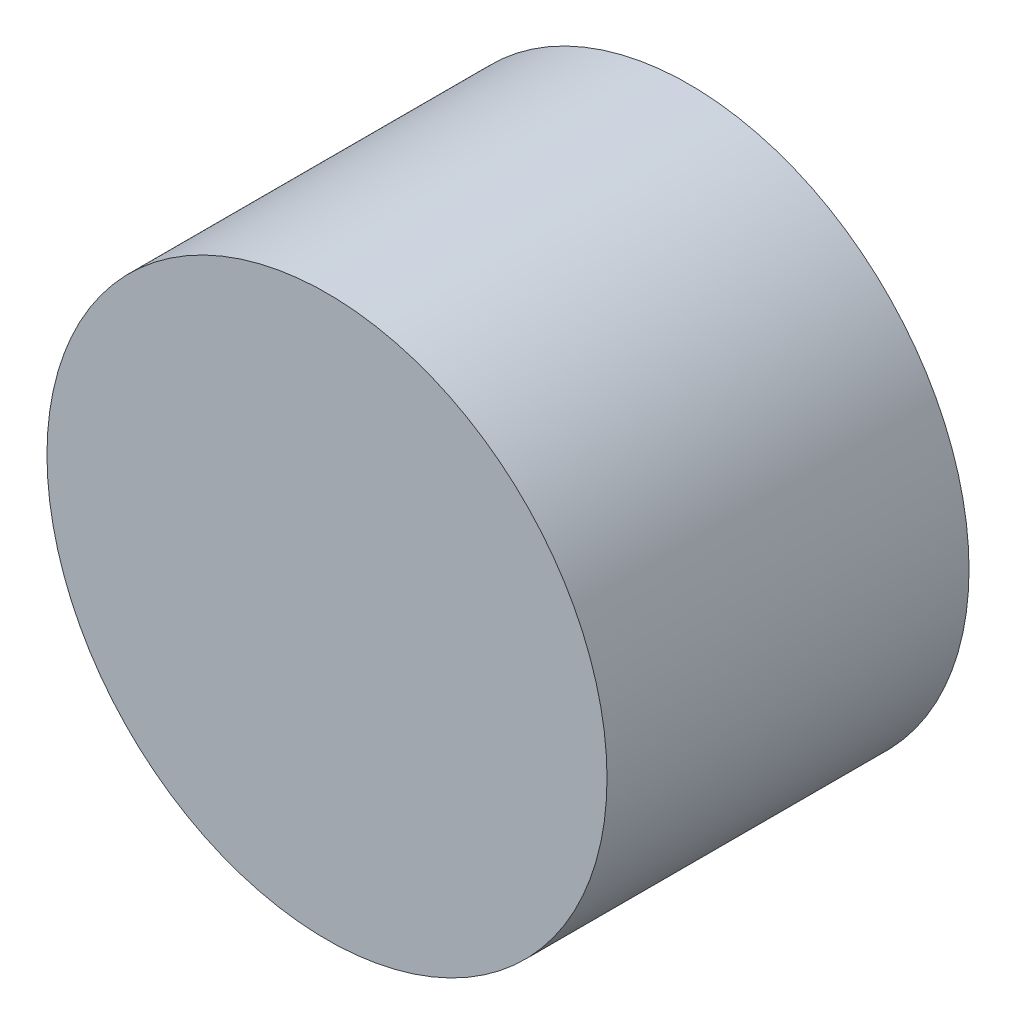
SolidWorks part; units mm, degrees
ref_plane "Front Plane" through (0, 0, 0) normal (0, 0, 1) x (1, 0, 0)
ref_plane "Top Plane" through (0, 0, 0) normal (0, 1, 0) x (1, 0, 0)
ref_plane "Right Plane" through (0, 0, 0) normal (1, 0, 0) x (0, 0, -1)
sketch "Sketch1" plane through (0, 0, 0) normal (0, 0, 1) x (1, 0, 0)
  circle A0 centre (0, 0) radius 8.509
  dimension "D1" = 17.018
extrude "Boss-Extrude1" add sketch "Sketch1" along normal blind 11
